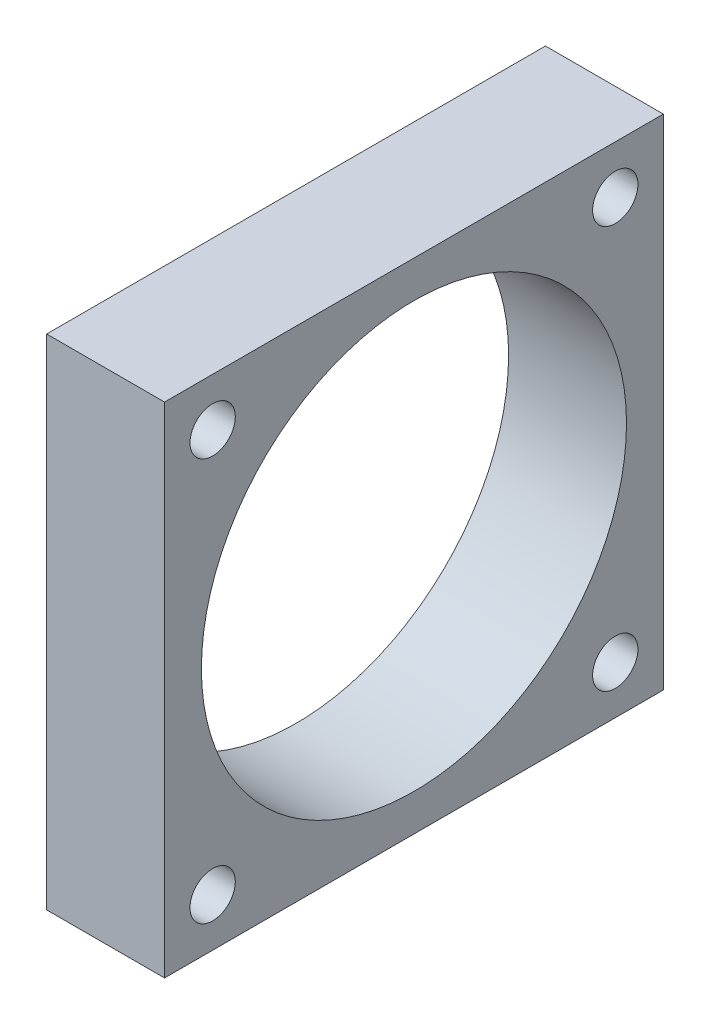
SolidWorks part; units mm, degrees
material "6061 Alloy"
ref_plane "Front Plane" through (0, 0, 0) normal (0, 0, 1) x (1, 0, 0)
ref_plane "Top Plane" through (0, 0, 0) normal (0, 1, 0) x (1, 0, 0)
ref_plane "Right Plane" through (0, 0, 0) normal (1, 0, 0) x (0, 0, -1)
sketch "Sketch1" plane through (0, 0, 0) normal (1, 0, 0) x (0, 0, -1)
  line L1 (-27.94, 27.94) -> (27.94, 27.94)
  line L2 (-27.94, 27.94) -> (-27.94, -27.94)
  line L3 (-27.94, -27.94) -> (27.94, -27.94)
  line L4 (27.94, 27.94) -> (27.94, -27.94)
  line L5 (-27.94, 27.94) -> (27.94, -27.94) construction
  line L6 (-27.94, -27.94) -> (27.94, 27.94) construction
  circle A0 centre (0, 0) radius 23.8125
  point P0 (0, 0)
  dimension "D1" = 47.625
  dimension "D2" = 55.88
  dimension "D3" = 55.88
extrude "Boss-Extrude1" add sketch "Sketch1" along normal blind 13.208
sketch "Sketch5" plane through (0, 0, 0) normal (1, 0, 0) x (0, 0, -1)
  line L0 (-27.94, -27.94) -> (0, 0) construction
  line L1 (-27.94, 27.94) -> (-27.94, -27.94) construction
  line L2 (-27.94, 27.94) -> (-27.94, -27.94) construction
  circle A0 centre (-22.5518, -22.5518) radius 2.54
  circle A1 centre (-22.5518, 22.5518) radius 2.54
  circle A2 centre (22.5518, 22.5518) radius 2.54
  circle A3 centre (22.5518, -22.5518) radius 2.54
  point P2 (39.4658, 25.1269)
  point P7 (0, 0)
  point P15 (0, 0)
  dimension "D1" = 5.08
  dimension "D2" = 7.62
  dimension "D3" = 4
extrude "Cut-Extrude2" cut sketch "Sketch5" against normal through all and the other way through all
